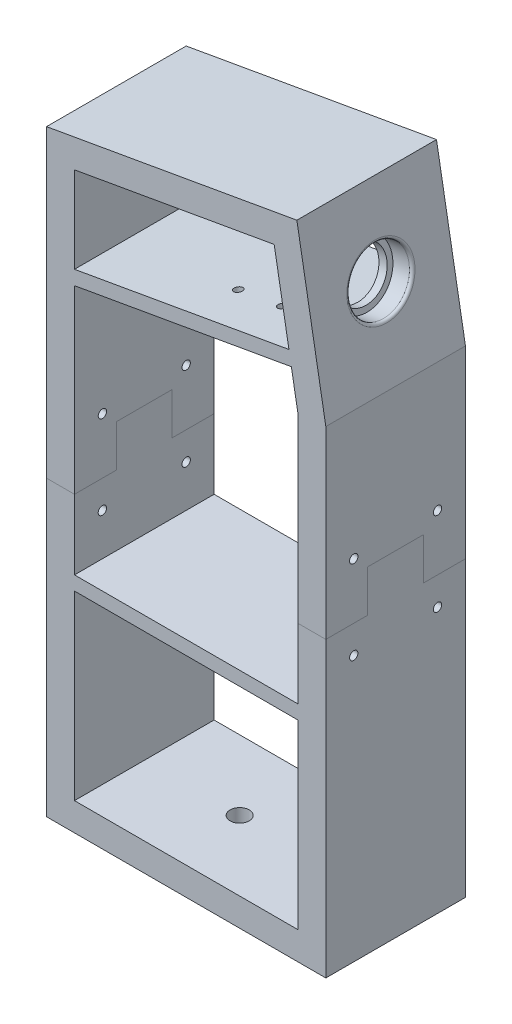
SolidWorks part; units mm, degrees
ref_plane "Front Plane" through (0, 0, 0) normal (0, 0, 1) x (1, 0, 0)
ref_plane "Top Plane" through (0, 0, 0) normal (0, 1, 0) x (1, 0, 0)
ref_plane "Right Plane" through (0, 0, 0) normal (1, 0, 0) x (0, 0, -1)
sketch "Sketch2" plane through (0, 0, 0) normal (0, 0, 1) x (1, 0, 0)
  line L6 (-50, 214.01) -> (-50, 0)
  line L8 (-50, 0) -> (50, 0)
  line L10 (-40, 205.619) -> (-40, 10)
  line L11 (-40, 10) -> (40, 10)
  line L12 (50, 0) -> (50, 171.01)
  line L13 (50, 171.01) -> (39.6312, 229.8144)
  line L14 (50, 171.01) -> (50, 266.0824) construction
  line L15 (39.6312, 229.8144) -> (-50, 214.01)
  line L16 (40, 10) -> (40, 170.1351)
  line L17 (40, 170.1351) -> (31.5196, 218.2298)
  line L18 (31.5196, 218.2298) -> (-40, 205.619)
  dimension "D1" = 171.01
  dimension "D2" = 100
  dimension "D3" = 10
  dimension "D4" = 214.01
  dimension "D6" = 10
extrude "Boss-Extrude1" add sketch "Sketch2" along normal blind 50
sketch "Sketch4" plane through (77.7367, 13.7071, 0) normal (0.9848, 0.1736, 0) x (0, 0, -1)
  line L0 (-25, 159.7296) -> (-25, 190.0581) construction
  line L1 (-50, 159.7296) -> (0, 159.7296) construction
  line L2 (-50, 219.4411) -> (0, 219.4411) construction
  circle A0 centre (-25, 190.0581) radius 11.025
  dimension "D1" = 22.05
  dimension "D2" = 29.383
extrude "Cut-Extrude1" cut sketch "Sketch4" against normal blind 7
sketch "Sketch5" plane through (70.8431, 12.4915, 0) normal (0.9848, 0.1736, 0) x (0, 0, -1)
  line L0 (-25, 201.0831) -> (-25, 179.0331) construction
  circle A0 centre (-25, 190.0581) radius 11.025 construction
  circle A1 centre (-25, 190.0581) radius 11.025 construction
  circle A2 centre (-25, 190.0581) radius 9
  dimension "D1" = 18
extrude "Cut-Extrude2" cut sketch "Sketch5" against normal blind 7
sketch "Sketch7" plane through (0, 0, 50) normal (0, 0, 1) x (1, 0, 0)
  line L0 (40, 170.1351) -> (31.5196, 218.2298) construction
  line L5 (36.795, 188.3114) -> (37.6633, 183.3873)
  line L7 (-40, 169.6932) -> (-40, 174.7703)
  line L10 (36.795, 188.3114) -> (-40, 174.7703)
  line L11 (-40, 169.6932) -> (37.6633, 183.3873)
  line L12 (-40, 205.619) -> (-40, 10) construction
  line L13 (31.5196, 218.2298) -> (-40, 205.619) construction
  dimension "D1" = 30.38
  dimension "D3" = 5
extrude "Boss-Extrude2" add sketch "Sketch7" against normal blind 50
sketch "Sketch8" plane through (-50, 0, 0) normal (-1, 0, 0) x (0, 0, 1)
  line L0 (50, 214.01) -> (0, 214.01) construction
  line L1 (50, 214.01) -> (50, 0) construction
  line L3 (0, 214.01) -> (0, 0) construction
  line L4 (0, 193.1639) -> (50, 193.1639) construction
  circle A0 centre (25, 193.1639) radius 5
  dimension "D1" = 10
  dimension "D2" = 20.8461
extrude "Cut-Extrude3" cut sketch "Sketch8" against normal blind 10
sketch "Sketch9" plane through (125.115, 198.8074, 0) normal (-0.1736, 0.9848, 0) x (-0.9848, -0.1736, 0)
  line L0 (78.8008, 25) -> (106.8793, 25) construction
  line L3 (106.8793, 34.6) -> (122.8793, 34.6) construction
  line L5 (78.8008, 50) -> (78.8008, 0) construction
  line L6 (106.8793, 25) -> (106.8793, 34.6) construction
  line L7 (106.8793, 25) -> (106.8793, 15.4) construction
  line L8 (122.8793, 34.6) -> (122.8793, 15.4) construction
  line L10 (122.8793, 15.4) -> (106.8793, 15.4) construction
  circle A0 centre (106.8793, 15.4) radius 1.485
  circle A1 centre (106.8793, 34.6) radius 1.485
  circle A2 centre (122.8793, 34.6) radius 1.485
  circle A3 centre (122.8793, 15.4) radius 1.485
  dimension "D1" = 28.0785
  dimension "D2" = 2.97
  dimension "D3" = 19.2
  dimension "D4" = 16
extrude "Cut-Extrude4" cut sketch "Sketch9" along normal up to next contours A3
sketch "Sketch10" plane through (0, 10, 0) normal (0, 1, 0) x (1, 0, 0)
  line L0 (50, -25) -> (24.131, -25) construction
  line L1 (-30.869, -50) -> (-30.869, 0) construction
  line L2 (50, -50) -> (50, 0) construction
  line L3 (-30, -25) -> (-5.8513, -25) construction
  circle A0 centre (-5.8513, -25) radius 3.425
  circle A1 centre (24.131, -25) radius 3.425
  dimension "D1" = 6.85
  dimension "D2" = 6.85
  dimension "D3" = 25.0177
  dimension "D4" = 55
extrude "Cut-Extrude5" cut sketch "Sketch10" against normal blind 10
sketch "Sketch11" plane through (0, 0, 50) normal (0, 0, 1) x (1, 0, 0)
  line L0 (-40, 75) -> (40, 75)
  line L3 (40, 75) -> (40, 80)
  line L4 (40, 80) -> (-40, 80)
  line L5 (-40, 80) -> (-40, 75)
  line L6 (-40, 169.6932) -> (-40, 10) construction
  line L7 (40, 10) -> (40, 170.1351) construction
  dimension "D1" = 5
  dimension "D2" = 75
extrude "Boss-Extrude3" add sketch "Sketch11" against normal blind 50
fillet "Fillet1" radius 1 1 edges at (42.819, 211.7353, 25)
sketch "Sketch14" plane through (-50, 0, 0) normal (-1, 0, 0) x (0, 0, 1)
  line L0 (0, 0) -> (0, 105) construction
  line L1 (0, 214.01) -> (0, 0) construction
  line L2 (0, 105) -> (50, 105) construction
  line L3 (50, 214.01) -> (50, 0) construction
  line L4 (50, 105) -> (50, 125) construction
  line L5 (50, 105) -> (50, 95) construction
  line L6 (50, 125) -> (40, 125) construction
  line L7 (50, 95) -> (40, 95) construction
  line L8 (25, 0) -> (25, 105) construction
  line L10 (50, 0) -> (0, 0) construction
  circle A0 centre (40, 125) radius 1.5
  circle A1 centre (40, 95) radius 1.5
  circle A2 centre (10, 95) radius 1.5
  circle A3 centre (10, 125) radius 1.5
  dimension "D1" = 3
  dimension "D2" = 3
  dimension "D3" = 95
  dimension "D4" = 125
  dimension "D5" = 15
extrude "Cut-Extrude6" cut sketch "Sketch14" against normal through all
sketch "Sketch15" plane through (-50, 0, 0) normal (-1, 0, 0) x (0, 0, 1)
  line L0 (0, 0) -> (0, 105) construction
  line L1 (0, 214.01) -> (0, 0) construction
  line L2 (0, 105) -> (15, 105)
  line L3 (15, 105) -> (15, 120)
  line L4 (15, 120) -> (35, 120)
  line L5 (35, 120) -> (35, 105)
  line L6 (35, 105) -> (50, 105)
  line L7 (50, 214.01) -> (50, 0) construction
  line L8 (50, 0) -> (0, 0) construction
  dimension "D1" = 15
  dimension "D2" = 35
  dimension "D3" = 15
  dimension "D4" = 105
  dimension "D5" = 105
split "Split1" trim tools "Sketch15" bodies to split 116 resulting bodies 117 118
